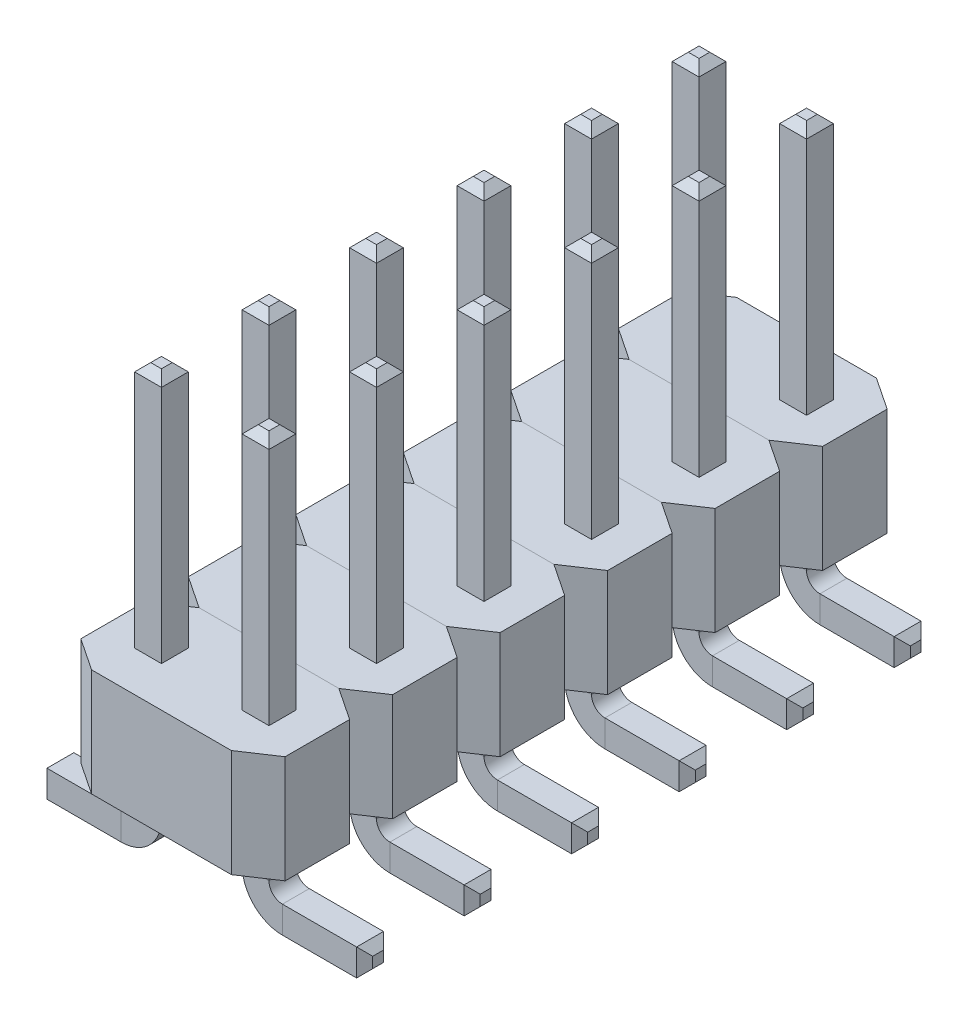
SolidWorks part; units mm, degrees
ref_plane "Front Plane" through (0, 0, 0) normal (0, 0, 1) x (1, 0, 0)
ref_plane "Top Plane" through (0, 0, 0) normal (0, 1, 0) x (1, 0, 0)
ref_plane "Right Plane" through (0, 0, 0) normal (1, 0, 0) x (0, 0, -1)
sketch "Sketch1" plane through (0, 0, 0) normal (0, 1, 0) x (1, 0, 0)
  line L0 (-2.413, -0.762) -> (-1.651, -1.27)
  line L1 (-1.651, -1.27) -> (1.651, -1.27)
  line L2 (-2.413, -0.762) -> (-2.413, 0.762)
  line L3 (-1.651, 1.27) -> (1.651, 1.27)
  line L4 (2.413, -0.762) -> (2.413, 0.762)
  line L5 (-2.413, -1.27) -> (2.413, 1.27) construction
  line L6 (-2.413, 1.27) -> (2.413, -1.27) construction
  line L7 (1.651, -1.27) -> (2.413, -0.762)
  line L8 (-2.413, 0.762) -> (-1.651, 1.27)
  line L9 (1.651, 1.27) -> (2.413, 0.762)
  point P0 (0, 0)
  dimension "D1" = 2.54
  dimension "D2" = 4.826
  dimension "D3" = 0.762
  dimension "D4" = 0.508
  dimension "D5" = 0.762
  dimension "D6" = 0.508
  dimension "D7" = 0.508
  dimension "D8" = 0.762
  dimension "D9" = 0.762
  dimension "D10" = 0.508
extrude "Boss-Extrude2" add sketch "Sketch1" along normal blind 2.54
sketch "Sketch2" plane through (0, 0, 0) normal (0, 0, 1) x (1, 0, 0)
  line L0 (-1.27, 2.54) -> (-1.27, 8.382)
  line L1 (0, -1.397) -> (0, 1.397) construction
  line L2 (1.27, 2.54) -> (1.27, 8.382)
  line L3 (-1.27, 2.54) -> (-1.27, -0.635)
  line L4 (-1.905, -1.27) -> (-3.8481, -1.27)
  line L7 (-1.651, 2.54) -> (1.651, 2.54) construction
  line L8 (0, 0) -> (0, 4.2903) construction
  line L9 (1.905, -1.27) -> (3.8481, -1.27)
  line L10 (1.27, 2.54) -> (1.27, -0.635)
  line L11 (-1.651, 0) -> (-2.413, 0) construction
  arc A1 (-1.27, -0.635) -> (-1.905, -1.27) centre (-1.905, -0.635) cw
  arc A2 (1.27, -0.635) -> (1.905, -1.27) centre (1.905, -0.635) ccw
  dimension "D3" = 0.635
  dimension "D1" = 2.54
  dimension "D2" = 5.842
  dimension "D4" = 7.6962
  dimension "D5" = 1.27
ref_plane "Plane1" through (0, 8.382, 0) normal (0, 1, 0) x (1, 0, 0)
sketch "Sketch3" plane through (0, 8.382, 0) normal (0, 1, 0) x (1, 0, 0)
  line L0 (0, -1.397) -> (0, 1.397) construction
  line L1 (-1.5875, -0.3175) -> (-0.9525, -0.3175)
  line L2 (-1.5875, -0.3175) -> (-1.5875, 0.3175)
  line L3 (-1.5875, 0.3175) -> (-0.9525, 0.3175)
  line L4 (-0.9525, -0.3175) -> (-0.9525, 0.3175)
  line L5 (-1.5875, -0.3175) -> (-0.9525, 0.3175) construction
  line L6 (-1.5875, 0.3175) -> (-0.9525, -0.3175) construction
  line L7 (1.5875, 0.3175) -> (0.9525, -0.3175) construction
  line L8 (1.5875, -0.3175) -> (0.9525, 0.3175) construction
  line L9 (0.9525, -0.3175) -> (0.9525, 0.3175)
  line L10 (1.5875, 0.3175) -> (0.9525, 0.3175)
  line L11 (1.5875, -0.3175) -> (1.5875, 0.3175)
  line L12 (1.5875, -0.3175) -> (0.9525, -0.3175)
  point P0 (-1.27, 0)
  point P12 (1.27, 0)
  dimension "D1" = 0.635
sketch "Sketch5" plane through (0, 8.382, 0) normal (0, 1, 0) x (1, 0, 0)
  line L0 (-1.5875, 0.3175) -> (-0.9525, 0.3175) construction
  line L1 (-0.9525, -0.3175) -> (-0.9525, 0.3175) construction
  line L2 (-1.5875, -0.3175) -> (-0.9525, -0.3175) construction
  line L3 (-1.5875, -0.3175) -> (-1.5875, 0.3175) construction
  line L4 (-1.5875, 0.3175) -> (-0.9525, 0.3175)
  line L5 (-0.9525, -0.3175) -> (-0.9525, 0.3175)
  line L6 (-1.5875, -0.3175) -> (-0.9525, -0.3175)
  line L7 (-1.5875, -0.3175) -> (-1.5875, 0.3175)
sketch "Sketch6" plane through (0, 8.382, 0) normal (0, 1, 0) x (1, 0, 0)
  line L0 (1.5875, 0.3175) -> (0.9525, 0.3175) construction
  line L1 (1.5875, -0.3175) -> (1.5875, 0.3175) construction
  line L2 (1.5875, -0.3175) -> (0.9525, -0.3175) construction
  line L3 (0.9525, -0.3175) -> (0.9525, 0.3175) construction
  line L4 (1.5875, 0.3175) -> (0.9525, 0.3175)
  line L5 (1.5875, -0.3175) -> (1.5875, 0.3175)
  line L6 (1.5875, -0.3175) -> (0.9525, -0.3175)
  line L7 (0.9525, -0.3175) -> (0.9525, 0.3175)
sweep "Sweep5" add profiles "Sketch5" path "Sketch2"
sketch "Sketch7" plane through (0, 0, 0) normal (0, 0, 1) x (1, 0, 0)
  line L3 (1.27, 2.54) -> (1.27, 8.382) construction
  line L4 (1.27, 2.54) -> (1.27, -0.635) construction
  line L5 (1.905, -1.27) -> (3.8481, -1.27) construction
  line L6 (1.27, 2.54) -> (1.27, 8.382)
  line L7 (1.27, 2.54) -> (1.27, -0.635)
  line L8 (1.905, -1.27) -> (3.8481, -1.27)
  arc A1 (1.27, -0.635) -> (1.905, -1.27) centre (1.905, -0.635) ccw construction
  arc A2 (1.27, -0.635) -> (1.905, -1.27) centre (1.905, -0.635) ccw
sweep "Sweep6" add profiles "Sketch6" path "Sketch7"
chamfer "Chamfer1" distance 0.1905 angle 45 16 edges at (-3.8481, -0.9525, 0) (-3.8481, -1.27, 0.3175) (-3.8481, -1.5875, 0) (-3.8481, -1.27, -0.3175) (-0.9525, 8.382, 0) (-1.27, 8.382, 0.3175) (-1.5875, 8.382, 0) (-1.27, 8.382, -0.3175) (3.8481, -1.27, -0.3175) (3.8481, -1.5875, 0) (3.8481, -1.27, 0.3175) (3.8481, -0.9525, 0) (1.27, 8.382, 0.3175) (0.9525, 8.382, 0) (1.27, 8.382, -0.3175) (1.5875, 8.382, 0)
sketch "Sketch8" plane through (0, 8.382, 0) normal (0, 1, 0) x (1, 0, 0)
  line L5 (-1.397, 0.127) -> (-1.143, -0.127) construction
  point P0 (-1.27, 0)
pattern_linear "LPattern1" count 6 spacing 2.54 along (0, 0, -1) of bodies 105
ref_plane "Plane2" through (0, 0, -6.35) normal (0, 0, 1) x (1, 0, 0)
